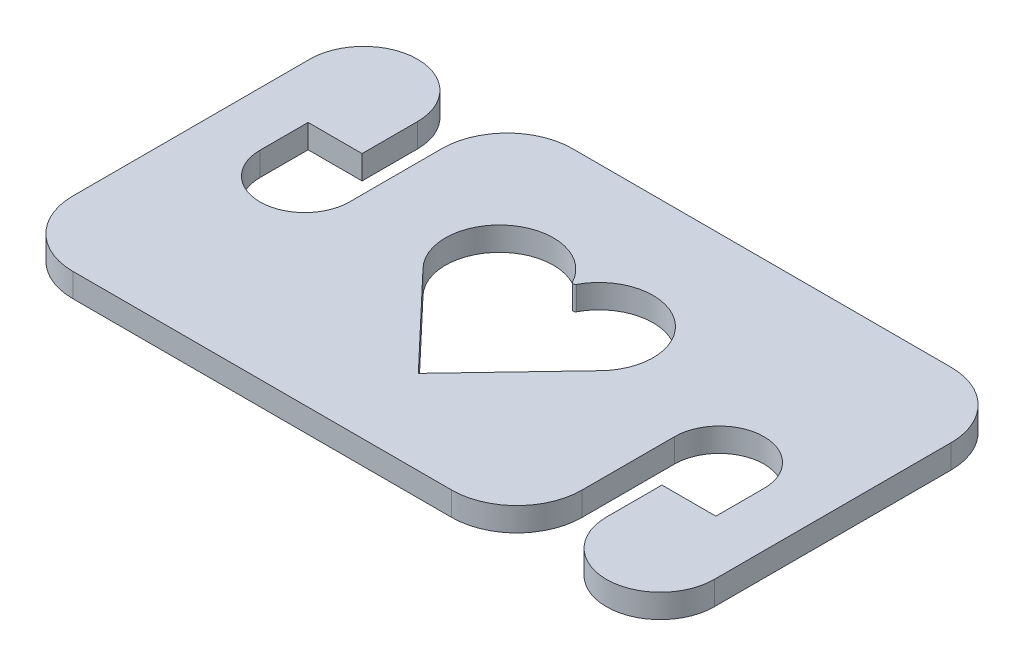
SolidWorks part; units mm, degrees
ref_plane "Front Plane" through (0, 0, 0) normal (0, 0, 1) x (1, 0, 0)
ref_plane "Top Plane" through (0, 0, 0) normal (0, 1, 0) x (1, 0, 0)
ref_plane "Right Plane" through (0, 0, 0) normal (1, 0, 0) x (0, 0, -1)
sketch "Sketch2" plane through (0, 0, 0) normal (0, 1, 0) x (1, 0, 0)
  line L0 (0, 0.5) -> (0, 20.4551)
  line L20 (9.0898, 20.4551) -> (9.0898, 15.7766)
  line L21 (9.0898, 15.7766) -> (4.5449, 15.7766)
  line L22 (4.5449, 15.7766) -> (4.5449, 11.7197)
  line L23 (12.0898, 11.7197) -> (12.0898, 19.5)
  line L24 (17.5898, 25) -> (27.5, 25)
  line L25 (5.5, -5) -> (27.5, -5)
  line L26 (27.5, 25) -> (27.5, -5) construction
  line L38 (27.5, 10) -> (0, 10) construction
  line L39 (37.4102, -5) -> (27.5, -5)
  line L40 (42.9102, 8.2803) -> (42.9102, 0.5)
  line L41 (50.4551, 4.2234) -> (50.4551, 8.2803)
  line L42 (45.9102, 4.2234) -> (50.4551, 4.2234)
  line L43 (45.9102, -0.4551) -> (45.9102, 4.2234)
  line L44 (55, 19.5) -> (55, -0.4551)
  line L45 (49.5, 25) -> (27.5, 25)
  arc A0 (0, 20.4551) -> (9.0898, 20.4551) centre (4.5449, 20.4551) cw
  arc A1 (4.5449, 11.7197) -> (12.0898, 11.7197) centre (8.3173, 11.7197) ccw
  arc A9 (0, 0.5) -> (5.5, -5) centre (5.5, 0.5) ccw
  arc A10 (12.0898, 19.5) -> (17.5898, 25) centre (17.5898, 19.5) cw
  arc A11 (42.9102, 0.5) -> (37.4102, -5) centre (37.4102, 0.5) cw
  arc A12 (50.4551, 8.2803) -> (42.9102, 8.2803) centre (46.6827, 8.2803) ccw
  arc A13 (55, -0.4551) -> (45.9102, -0.4551) centre (50.4551, -0.4551) cw
  arc A14 (55, 19.5) -> (49.5, 25) centre (49.5, 19.5) ccw
  point P19 (0, 0)
  point P22 (11.4758, 25)
  dimension "D1" = 5.5
  dimension "D3" = 2
  dimension "D6" = 4.5449
  dimension "D9" = 3.7724
  dimension "D2" = 30
  dimension "D5" = 3
extrude "Boss-Extrude1" add sketch "Sketch2" along normal blind 2 contours L23 A10 L24 L45 A14 L44 A13 L43 L42 L41 A12 L40 A11 L39 L25 A9 L0 A0 L20 L21 L22 A1
sketch "Sketch3" plane through (0, 2, 0) normal (0, 1, 0) x (1, 0, 0)
  line L0 (0, 10) -> (55, 10) construction
  line L1 (0, 0.5) -> (0, 20.4551) construction
  line L2 (55, 19.5) -> (55, -0.4551) construction
  line L3 (37.4102, -5) -> (5.5, -5) construction
  line L4 (27.5, 2.1073) -> (20.0019, 10)
  line L5 (27.5, -5) -> (27.5, 25) construction
  line L6 (17.5898, 25) -> (49.5, 25) construction
  line L8 (27.5, 2.1073) -> (34.9981, 10)
  arc A0 (20.0019, 10) -> (27.5, 14.9051) centre (23.3035, 13.1365) cw
  arc A1 (34.9981, 10) -> (27.5, 14.9051) centre (31.6965, 13.1365) ccw
  point P15 (27.5, 14.9051)
  point P16 (20.5093, 10)
  point P17 (27.2181, 2.671)
  point P18 (27.5, 14.0292)
  point P19 (27.5, 1.318)
  point P20 (19.7764, 10)
  point P21 (27.5, 13.89)
  point P22 (27.5, 2.1073)
  point P23 (20.0019, 10)
  dimension "D1" = 15
  dimension "D2" = 27.5
extrude "Cut-Extrude1" cut sketch "Sketch3" against normal through all
fillet "Fillet1" radius 0.2 1 edges at (27.5, 1, -14.9051)
